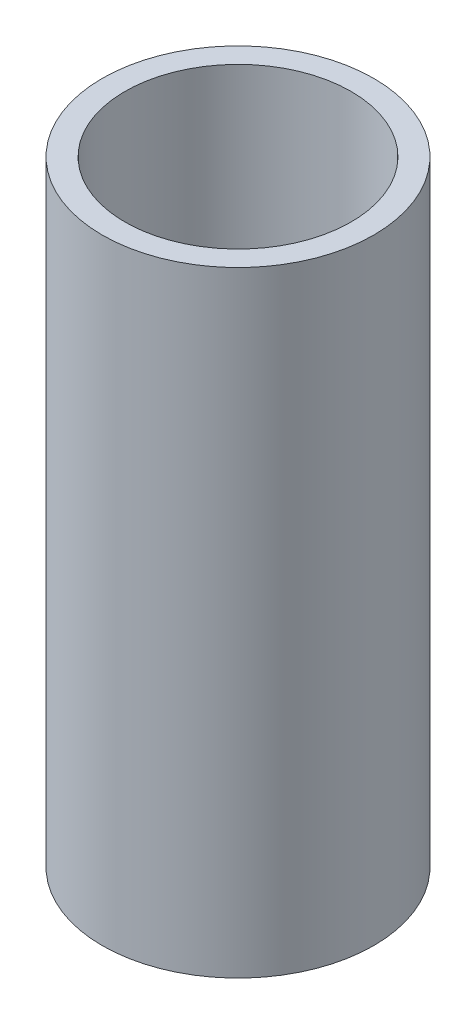
SolidWorks part; units mm, degrees
ref_plane "Alzado" through (0, 0, 0) normal (0, 0, 1) x (1, 0, 0)
ref_plane "Planta" through (0, 0, 0) normal (0, 1, 0) x (1, 0, 0)
ref_plane "Vista lateral" through (0, 0, 0) normal (1, 0, 0) x (0, 0, -1)
sketch "Croquis1" plane through (0, 0, 0) normal (0, 0, 1) x (1, 0, 0)
  line L0 (0, 0) -> (0, 238) construction
  line L1 (-43.75, 238) -> (-52.5, 238)
  line L2 (-52.5, 238) -> (-52.5, 0)
  line L3 (-52.5, 0) -> (-43.75, 0)
  line L4 (-43.75, 0) -> (-43.75, 238)
  point P3 (0, 0)
  dimension "D1" = 238
  dimension "D2" = 52.5
  dimension "D3" = 43.75
revolve "Revolución1" add sketch "Croquis1" angle 360 about L0
